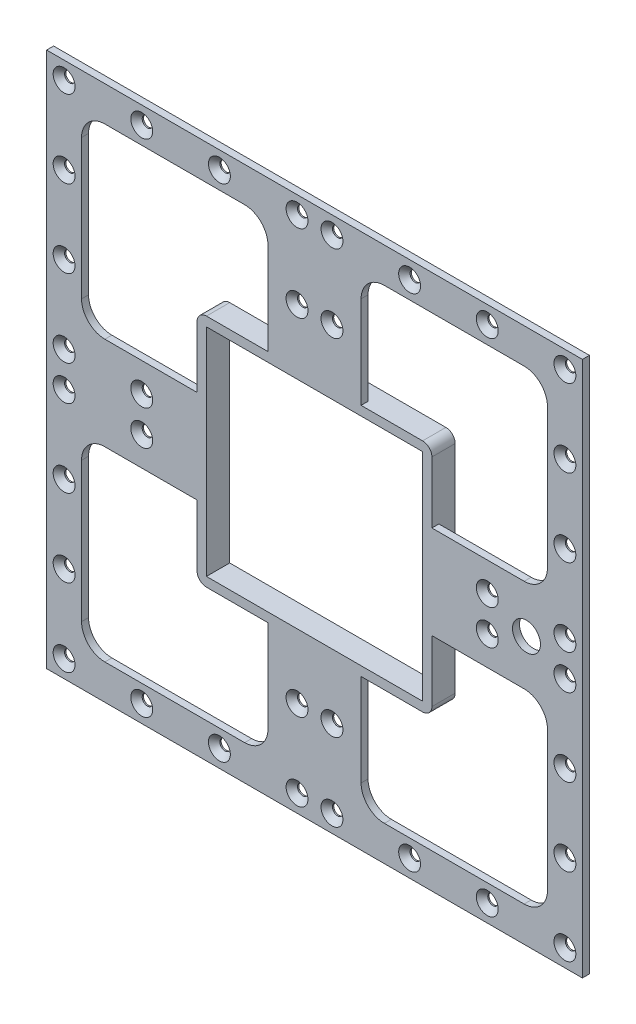
SolidWorks part; units mm, degrees
material "6061-T6 (SS)"
ref_plane "Alzado" through (0, 0, 0) normal (0, 0, 1) x (1, 0, 0)
ref_plane "Planta" through (0, 0, 0) normal (0, 1, 0) x (1, 0, 0)
ref_plane "Vista lateral" through (0, 0, 0) normal (1, 0, 0) x (0, 0, -1)
sketch "Sketch1" plane through (0, 0, 0) normal (0, 0, 1) x (1, 0, 0)
  line L1 (-115, 115) -> (115, 115)
  line L2 (-115, 115) -> (-115, -115)
  line L3 (-115, -115) -> (115, -115)
  line L4 (115, 115) -> (115, -115)
  line L5 (-115, 115) -> (115, -115) construction
  line L6 (-115, -115) -> (115, 115) construction
  point P0 (0, 0)
  dimension "D1" = 230
extrude "Boss-Extrude1" add sketch "Sketch1" along normal blind 3
sketch "Sketch2" plane through (0, 0, 0) normal (0, 0, 1) x (1, 0, 0)
  line L0 (-115, 115) -> (-115, -115) construction
  line L1 (-100, 100) -> (-20, 100)
  line L2 (-100, 100) -> (-100, 20)
  line L3 (-100, 20) -> (-20, 20)
  line L4 (-20, 100) -> (-20, 20)
  line L5 (-100, 100) -> (-20, 20) construction
  line L6 (-100, 20) -> (-20, 100) construction
  line L7 (115, 115) -> (-115, 115) construction
  point P0 (-60, 60)
  point P9 (-60, 100)
  dimension "D1" = 80
  dimension "D2" = 80
  dimension "D3" = 15
  dimension "D4" = 15
extrude "Cut-Extrude2" cut sketch "Sketch2" along normal through all
fillet "Fillet1" radius 10 4 edges at (-100, 100, 1.5) (-20, 100, 1.5) (-20, 20, 1.5) (-100, 20, 1.5)
pattern_linear "LPattern2" count 2 spacing 120 along (0, -1, 0) count 2 spacing 120 along (1, 0, 0) of "Fillet1", "Cut-Extrude2"
sketch "Sketch11" plane through (0, 0, 3) normal (0, 0, 1) x (1, 0, 0)
  line L0 (-115, 115) -> (-115, -115) construction
  line L1 (115, 115) -> (-115, 115) construction
  point P0 (-107.5, 107.5)
  dimension "D1" = 7.5
  dimension "D2" = 7.5
hole_wizard "CSK for M4 Flat Head Machine Screw4" positions "Sketch11" profile "Sketch12" countersink size "M4" standard "ANSI Metric" end condition through all
sketch "Sketch12" plane through (-107.5, 107.5, 3) normal (1, 0, 0) x (0, -1, 0)
  line L0 (0, 0) -> (0, 3)
  line L1 (0, 3) -> (2.25, 3)
  line L2 (2.25, 3) -> (2.25, 2.45)
  line L3 (2.25, 2.45) -> (4.7, 0)
  line L5 (4.7, 0) -> (0, 0)
  line L6 (-2.25, 2.45) -> (-4.7, 0) construction
  line L11 (0, -6.35) -> (0, 107.95) construction
  dimension "Thru Hole Dia." = 4.5
  dimension "Thru Hole Depth" = 3
  dimension "Near C'Sink Dia." = 9.4
  dimension "Near C'Sink Angle" = 90
sketch "Sketch13" plane through (0, 0, 3) normal (0, 0, 1) x (1, 0, 0)
  line L0 (0, 115) -> (0, -115) construction
  line L1 (115, 115) -> (-115, 115) construction
  line L2 (-115, -115) -> (115, -115) construction
  line L3 (-115, 0) -> (115, 0) construction
  line L4 (-115, 115) -> (-115, -115) construction
  line L5 (115, -115) -> (115, 115) construction
pattern_linear "LPattern8" count 4 spacing 33.3333 along (1, 0, 0) count 4 spacing 33.3333 along (0, -1, 0) skipping (1, 1), (1, 2), (2, 1), (2, 2) of "CSK for M4 Flat Head Machine Screw4"
mirror "Mirror1" about plane through (0, 0, 0) normal (1, 0, 0) of "LPattern8", "CSK for M4 Flat Head Machine Screw4" second plane through (0, 0, 0) second plane normal (0, 1, 0)
sketch "Sketch14" plane through (0, 0, 3) normal (0, 0, 1) x (1, 0, 0)
  line L1 (-49, 49) -> (49, 49)
  line L2 (-49, 49) -> (-49, -49)
  line L3 (-49, -49) -> (49, -49)
  line L4 (49, 49) -> (49, -49)
  line L5 (-49, 49) -> (49, -49) construction
  line L6 (-49, -49) -> (49, 49) construction
  point P0 (0, 0)
  dimension "D1" = 98
  dimension "D2" = 98
extrude "Cut-Extrude3" cut sketch "Sketch14" against normal up to next
sketch "Sketch15" plane through (0, 0, 3) normal (0, 0, 1) x (1, 0, 0)
  line L1 (-50.4, 50.4) -> (50.4, 50.4)
  line L2 (-50.4, 50.4) -> (-50.4, -50.4)
  line L3 (-50.4, -50.4) -> (50.4, -50.4)
  line L4 (50.4, 50.4) -> (50.4, -50.4)
  line L5 (-50.4, 50.4) -> (50.4, -50.4) construction
  line L6 (-50.4, -50.4) -> (50.4, 50.4) construction
  line L7 (-46.4, 46.4) -> (46.4, 46.4)
  line L8 (-46.4, 46.4) -> (-46.4, -46.4)
  line L9 (-46.4, -46.4) -> (46.4, -46.4)
  line L10 (46.4, 46.4) -> (46.4, -46.4)
  line L11 (-46.4, 46.4) -> (46.4, -46.4) construction
  line L12 (-46.4, -46.4) -> (46.4, 46.4) construction
  point P0 (0, 0)
  point P6 (0, 0)
  dimension "D1" = 92.8
  dimension "D2" = 4
extrude "Boss-Extrude2" add sketch "Sketch15" against normal blind 10
fillet "Fillet2" radius 4 4 edges at (-50.4, -50.4, -2) (50.4, -50.4, -2) (50.4, 50.4, -2) (-50.4, 50.4, -2)
sketch "Sketch16" plane through (0, 0, 3) normal (0, 0, 1) x (1, 0, 0)
  circle A0 centre (91, 0) radius 6
  dimension "D1" = 12
extrude "Cut-Extrude4" cut sketch "Sketch16" against normal up to next
